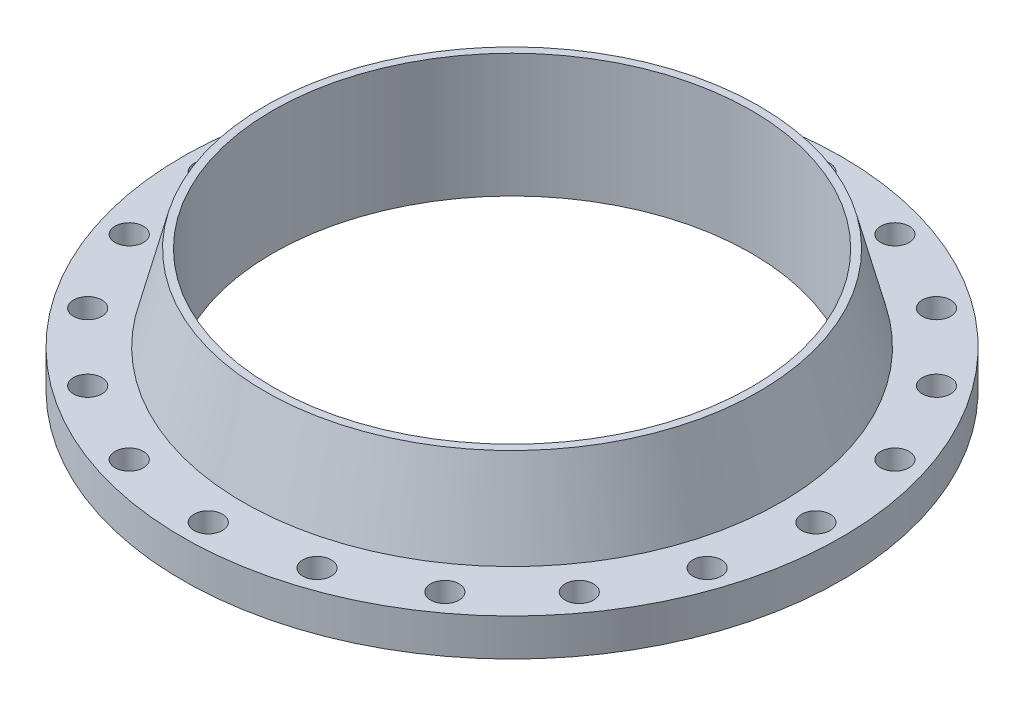
SolidWorks part; units mm, degrees
ref_plane "Front Plane" through (0, 0, 0) normal (0, 0, 1) x (1, 0, 0)
ref_plane "Top Plane" through (0, 0, 0) normal (0, 1, 0) x (1, 0, 0)
ref_plane "Right Plane" through (0, 0, 0) normal (1, 0, 0) x (0, 0, -1)
sketch "Sketch8" plane through (0, 0, 0) normal (0, 0, 1) x (1, 0, 0)
  line L0 (0, 0) -> (0, -0.0625) construction
  line L1 (-11.625, 0) -> (-11.625, 5.94)
  line L2 (-11.625, 0) -> (-11.625, -0.0625)
  line L3 (0, 0) -> (0, 10.2517) construction
  line L4 (-11.625, -0.0625) -> (-13.625, -0.0625)
  line L5 (-13.625, -0.0625) -> (-13.625, 0)
  line L8 (-13.625, 0) -> (-16, 0)
  line L9 (-16, 0) -> (-16, 1.81)
  line L10 (-16, 1.81) -> (-13.06, 1.81)
  line L12 (-12, 5.94) -> (-11.625, 5.94)
  line L14 (-12, 5.94) -> (-13.06, 1.81)
  dimension "D1" = 11.625
  dimension "D2" = 12
  dimension "D3" = 13.06
  dimension "D4" = 13.625
  dimension "D5" = 16
  dimension "D6" = 1.81
  dimension "D7" = 5.94
  dimension "D8" = 0.0625
revolve "Revolve1" add sketch "Sketch8" angle 360 about L3
sketch "Sketch10" plane through (0, 0, 0) normal (0, 1, 0) x (1, 0, 0)
  circle A0 centre (0, 14.75) radius 0.69
  dimension "D1" = 1.38
  dimension "D2" = 14.75
extrude "Cut-Extrude1" cut sketch "Sketch10" along normal blind 6.81
pattern_circular "CirPattern1" count 20 over 360 about axis through (0, 0, 0) along (0, 1, 0) of "Cut-Extrude1"
scale "Scale1" scale about centroid uniform scaling yes scale factor 25.4
